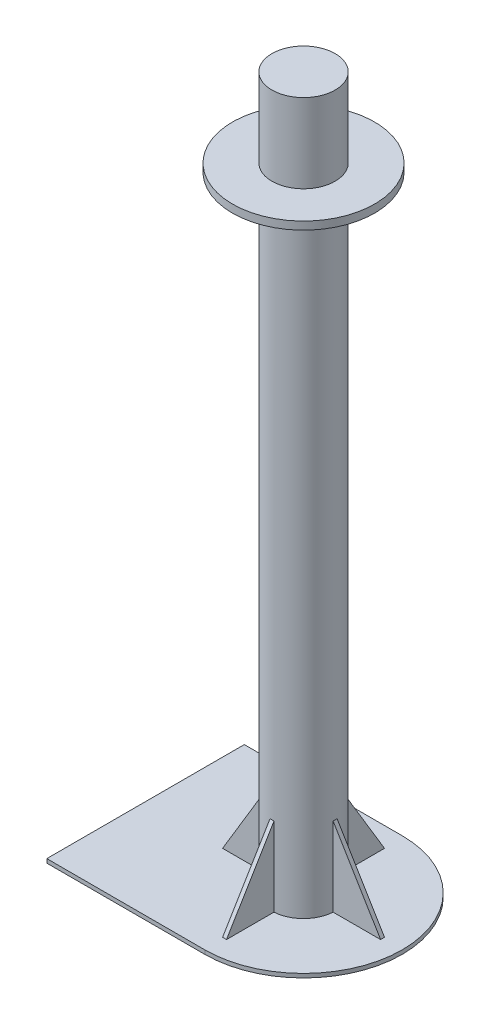
SolidWorks part; units mm, degrees
ref_plane "前视基准面" through (0, 0, 0) normal (0, 0, 1) x (1, 0, 0)
ref_plane "上视基准面" through (0, 0, 0) normal (0, 1, 0) x (1, 0, 0)
ref_plane "右视基准面" through (0, 0, 0) normal (1, 0, 0) x (0, 0, -1)
sketch "草图1" plane through (0, 0, 0) normal (0, 1, 0) x (1, 0, 0)
  line L1 (100, -125) -> (-100, -125)
  line L3 (100, 125) -> (-100, 125)
  line L4 (-100, -125) -> (-100, 125)
  arc A0 (100, -125) -> (100, 125) centre (100, 0) ccw
  point P0 (0, 0)
  point P8 (100, 0)
  dimension "D3" = 250
  dimension "D1" = 200
  dimension "D2" = 250
extrude "凸台-拉伸2" add sketch "草图1" along normal blind 5
sketch "草图5" plane through (0, 5, 0) normal (0, 1, 0) x (1, 0, 0)
  circle A0 centre (100, 0) radius 40
  dimension "D1" = 80
extrude "凸台-拉伸5" add sketch "草图5" along normal blind 100
sketch "草图6" plane through (0, 5, 0) normal (0, 1, 0) x (1, 0, 0)
  line L0 (100, -125) -> (100, -40) construction
  line L1 (225, 0) -> (140, 0) construction
  line L2 (-100, 125) -> (-100, -125) construction
  line L3 (102.5, -100) -> (97.5, -100)
  line L4 (0, -2.5) -> (0, 2.5)
  line L5 (102.5, 100) -> (97.5, 100)
  line L6 (200, -2.5) -> (200, 2.5)
  line L7 (200, -2.5) -> (139.9218, -2.5)
  line L8 (0, 2.5) -> (60.0782, 2.5)
  line L9 (102.5, -100) -> (102.5, -39.9218)
  line L10 (102.5, 100) -> (103.6086, 100.5651)
  line L11 (97.5, 100) -> (97.5, 39.9218)
  line L14 (97.5, -39.9218) -> (97.5, -100)
  line L15 (60.0782, -2.5) -> (0, -2.5)
  line L16 (60, 0) -> (-100, 0) construction
  line L19 (100, 40) -> (100, 125) construction
  line L20 (102.5, 39.9218) -> (102.5, 100)
  line L21 (139.9218, 2.5) -> (200, 2.5)
  arc A0 (100, -125) -> (100, 125) centre (100, 0) ccw construction
  arc A1 (139.9218, -2.5) -> (139.9218, 2.5) centre (100, 0) ccw
  arc A2 (97.5, -39.9218) -> (102.5, -39.9218) centre (100, 0) ccw
  arc A3 (102.5, 39.9218) -> (97.5, 39.9218) centre (100, 0) ccw
  arc A4 (60.0782, 2.5) -> (60.0782, -2.5) centre (100, 0) ccw
  point P23 (139.9218, -2.5)
  point P24 (139.9218, 2.5)
  point P25 (102.5, 39.9218)
  point P26 (97.5, 39.9218)
  point P27 (60.0782, -2.5)
  point P28 (97.5, -39.9218)
  point P29 (102.5, -39.9218)
  dimension "D12" = 80
  dimension "D1" = 5
  dimension "D2" = 2.5
  dimension "D3" = 5
  dimension "D4" = 2.5
  dimension "D5" = 2.5
  dimension "D6" = 5
  dimension "D7" = 2.5
  dimension "D8" = 5
  dimension "D9" = 100
  dimension "D10" = 100
  dimension "D11" = 100
extrude "凸台-拉伸6" add sketch "草图6" along normal blind 100 contours L14 L3 L9 A2 | L8 A4 L15 L4 | L5 L11 A3 L20 | L7 A1 L21 L6
sketch "草图7" plane through (97.5, 0, 0) normal (-1, 0, 0) x (0, 0, 1)
  line L0 (39.9218, 105) -> (100, 5)
  line L1 (100, 5) -> (100, 105)
  line L2 (100, 105) -> (39.9218, 105)
extrude "切除-拉伸1" cut sketch "草图7" against normal blind 10
sketch "草图8" plane through (0, 0, 2.5) normal (0, 0, 1) x (1, 0, 0)
  line L0 (139.9218, 105) -> (200, 5)
  line L1 (200, 105) -> (139.9218, 105) construction
  line L2 (139.9218, 105) -> (139.9218, 5) construction
  line L3 (200, 5) -> (200, 105)
  line L4 (200, 105) -> (139.9218, 105)
extrude "切除-拉伸2" cut sketch "草图8" against normal blind 10
sketch "草图9" plane through (102.5, 0, 0) normal (1, 0, 0) x (0, 0, -1)
  line L0 (39.9218, 105) -> (100, 105)
  line L1 (100, 105) -> (100, 5)
  line L2 (100, 5) -> (39.9218, 105)
extrude "切除-拉伸3" cut sketch "草图9" against normal blind 10
sketch "草图10" plane through (0, 0, -2.5) normal (0, 0, -1) x (-1, 0, 0)
  line L0 (0, 105) -> (0, 5)
  line L1 (0, 105) -> (0, 5) construction
  line L3 (0, 5) -> (-60.0782, 105)
  line L4 (-60.0782, 105) -> (0, 105)
extrude "切除-拉伸4" cut sketch "草图10" against normal blind 10
sketch "草图11" plane through (0, 105, 0) normal (0, 1, 0) x (1, 0, 0)
  circle A0 centre (100, 0) radius 40
extrude "凸台-拉伸7" add sketch "草图11" along normal blind 690
sketch "草图12" plane through (0, 795, 0) normal (0, 1, 0) x (1, 0, 0)
  circle A1 centre (100, 0) radius 90
  dimension "D1" = 180
extrude "凸台-拉伸8" add sketch "草图12" along normal blind 10
sketch "草图13" plane through (0, 805, 0) normal (0, 1, 0) x (1, 0, 0)
  circle A1 centre (100, 0) radius 40
  dimension "D1" = 80
extrude "凸台-拉伸9" add sketch "草图13" along normal blind 100
